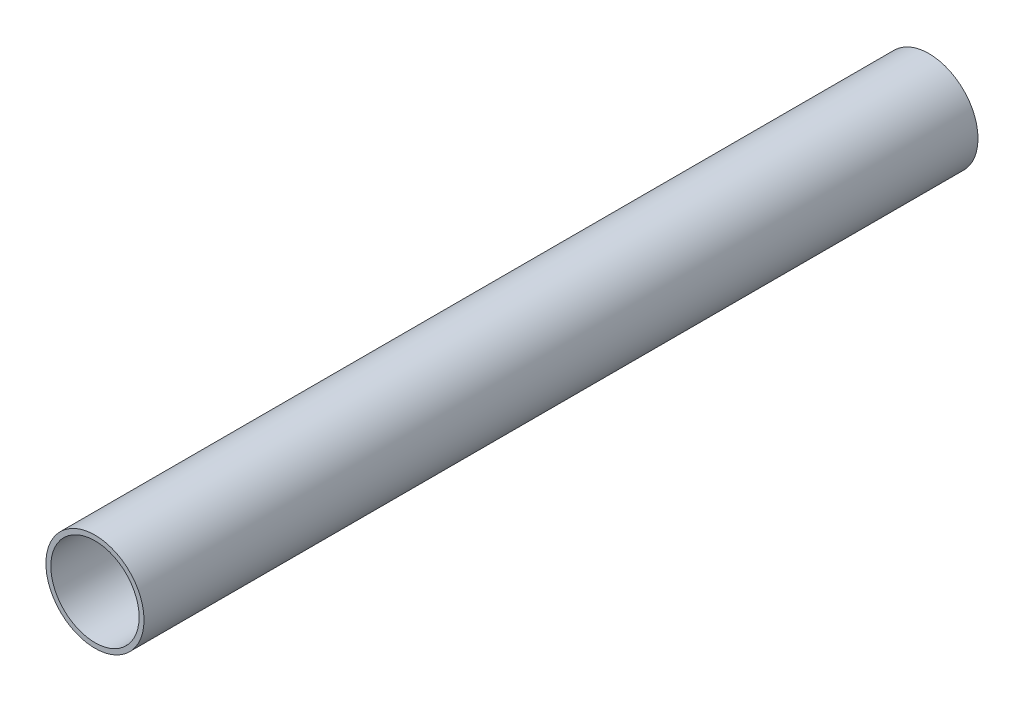
SolidWorks part; units mm, degrees
material "ABS"
ref_plane "Front Plane" through (0, 0, 0) normal (0, 0, 1) x (1, 0, 0)
ref_plane "Top Plane" through (0, 0, 0) normal (0, 1, 0) x (1, 0, 0)
ref_plane "Right Plane" through (0, 0, 0) normal (1, 0, 0) x (0, 0, -1)
sketch "Sketch3" plane through (0, 0, 0) normal (0, 0, 1) x (1, 0, 0)
  circle A0 centre (0, 0) radius 10
  dimension "D1" = 20
extrude "Extrude-Thin2" add sketch "Sketch3" along normal blind 170 thin contours A0 thin type one direction reverse wall 1
